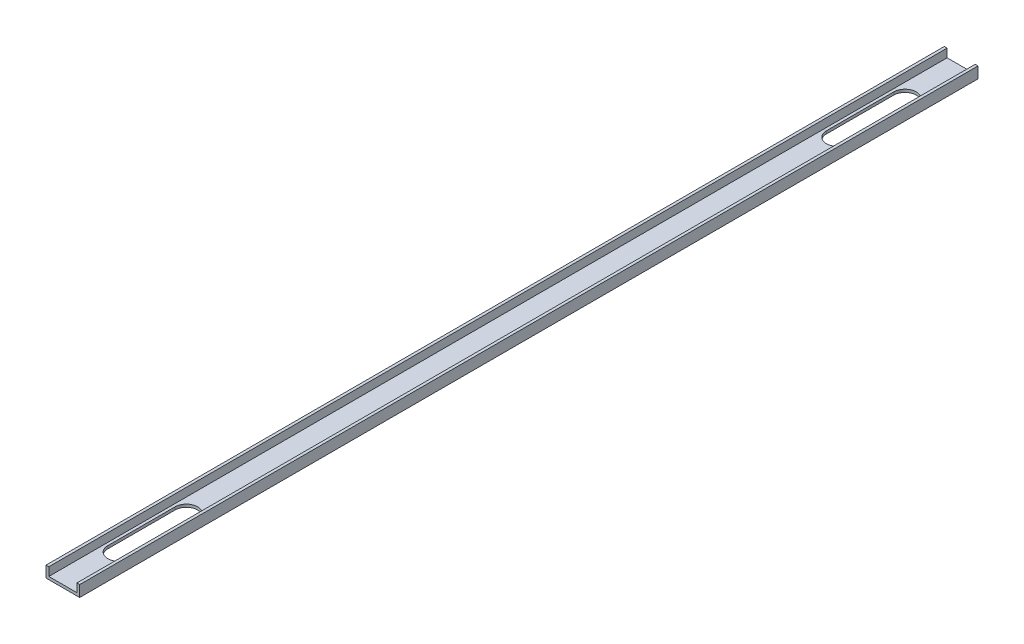
SolidWorks part; units mm, degrees
ref_plane "Front" through (0, 0, 0) normal (0, 0, 1) x (1, 0, 0)
ref_plane "Top" through (0, 0, 0) normal (0, 1, 0) x (1, 0, 0)
ref_plane "Right" through (0, 0, 0) normal (1, 0, 0) x (0, 0, -1)
sketch "Sketch1" plane through (0, 0, 0) normal (0, 0, 1) x (1, 0, 0)
  line L0 (3.175, 3.175) -> (3.175, 12.7)
  line L1 (0, 0) -> (38.1, 0)
  line L2 (0, 0) -> (0, 12.7)
  line L4 (38.1, 0) -> (38.1, 12.7)
  line L5 (3.175, 3.175) -> (34.925, 3.175)
  line L6 (34.925, 3.175) -> (34.925, 12.7)
  line L7 (0, 12.7) -> (3.175, 12.7)
  line L8 (38.1, 12.7) -> (34.925, 12.7)
  dimension "D1" = 12.7
  dimension "D2" = 38.1
  dimension "D3" = 3.175
extrude "f" add sketch "Sketch1" along normal blind 1016
sketch "Sketch2" plane through (0, 3.175, 0) normal (0, 1, 0) x (1, 0, 0)
  line L0 (3.175, -914.4) -> (34.925, -914.4) construction
  line L1 (3.175, -1016) -> (3.175, 0) construction
  line L2 (34.925, -1016) -> (34.925, 0) construction
  line L3 (19.05, -952.5) -> (19.05, -876.3) construction
  line L4 (6.35, -952.5) -> (6.35, -876.3)
  line L5 (31.75, -952.5) -> (31.75, -876.3)
  line L6 (34.925, -1016) -> (3.175, -1016) construction
  arc A0 (6.35, -952.5) -> (31.75, -952.5) centre (19.05, -952.5) ccw
  arc A1 (31.75, -876.3) -> (6.35, -876.3) centre (19.05, -876.3) ccw
  point P8 (19.05, -914.4)
  dimension "D1" = 76.2
  dimension "D2" = 101.6
extrude "Cut-Extrude1" cut sketch "Sketch2" against normal up to next (3.175 mm away)
ref_plane "Plane1" through (0, 0, 508) normal (0, 0, 1) x (1, 0, 0)
mirror "Mirror1" about plane through (0, 0, 508) normal (0, 0, 1) of "Cut-Extrude1"
